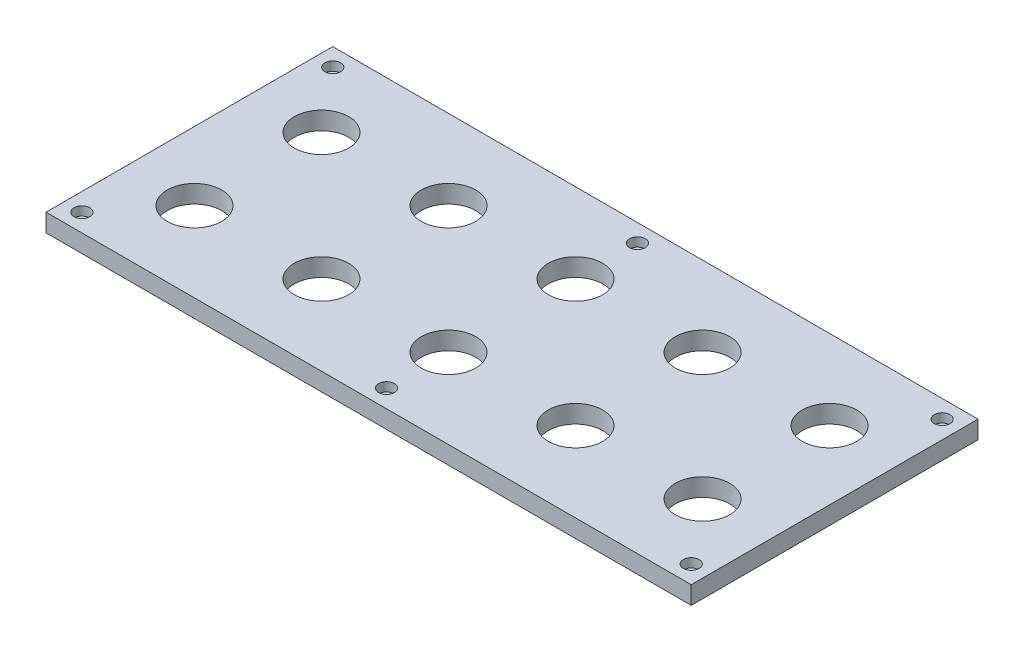
SolidWorks part; units mm, degrees
material "Ceramic Porcelain"
ref_plane "Front Plane" through (0, 0, 0) normal (0, 0, 1) x (1, 0, 0)
ref_plane "Top Plane" through (0, 0, 0) normal (0, 1, 0) x (1, 0, 0)
ref_plane "Right Plane" through (0, 0, 0) normal (1, 0, 0) x (0, 0, -1)
sketch "Sketch1" plane through (0, 0, 0) normal (0, 1, 0) x (1, 0, 0)
  line L1 (228.6, 101.6) -> (-228.6, 101.6)
  line L2 (228.6, 101.6) -> (228.6, -101.6)
  line L3 (228.6, -101.6) -> (-228.6, -101.6)
  line L4 (-228.6, 101.6) -> (-228.6, -101.6)
  line L5 (0, -101.6) -> (0, 101.6) construction
  line L6 (228.6, 0) -> (-228.6, 0) construction
  point P0 (0, 0)
  dimension "D1" = 457.2
  dimension "D2" = 203.2
extrude "Boss-Extrude1" add sketch "Sketch1" against normal blind 12.7
sketch "Sketch2" plane through (0, 0, 0) normal (0, 1, 0) x (1, 0, 0)
  circle A0 centre (-180, 45) radius 19.304 construction
  circle A1 centre (-90, 45) radius 19.304 construction
  circle A2 centre (0, 45) radius 19.304 construction
  circle A3 centre (-180, -45) radius 19.304 construction
  circle A4 centre (-90, -45) radius 19.304 construction
  circle A5 centre (0, -45) radius 19.304 construction
  circle A6 centre (90, -45) radius 19.304 construction
  circle A7 centre (90, 45) radius 19.304 construction
  circle A8 centre (180, 45) radius 19.304 construction
  circle A9 centre (180, -45) radius 19.304 construction
  circle A10 centre (-180, 45) radius 19.304
  circle A11 centre (-90, 45) radius 19.304
  circle A12 centre (0, 45) radius 19.304
  circle A13 centre (-180, -45) radius 19.304
  circle A14 centre (-90, -45) radius 19.304
  circle A15 centre (0, -45) radius 19.304
  circle A16 centre (90, -45) radius 19.304
  circle A17 centre (90, 45) radius 19.304
  circle A18 centre (180, 45) radius 19.304
  circle A19 centre (180, -45) radius 19.304
  point P0 (0, 88.9)
  point P2 (-215.9, 88.9)
  point P4 (215.9, 88.9)
  point P6 (215.9, -88.9)
  point P8 (0, -88.9)
  point P10 (-215.9, -88.9)
extrude "Cut-Extrude1" cut sketch "Sketch2" against normal up to next
hole_wizard "CBORE for 1/4 Socket Head Cap Screw1" positions "Sketch5" profile "Sketch6" counterbore size "1/4" standard "ANSI Inch" end condition up to next
sketch "Sketch5" plane through (0, 0, 0) normal (0, 1, 0) x (1, 0, 0)
  point P0 (-215.9, -88.9)
  point P3 (0, -88.9)
  point P6 (215.9, -88.9)
  point P9 (215.9, 88.9)
  point P12 (0, 88.9)
  point P15 (-215.9, 88.9)
sketch "Sketch6" plane through (-215.9, 0, 88.9) normal (1, 0, 0) x (0, 0, 1)
  line L0 (0, 0) -> (0, 12.7)
  line L1 (0, 12.7) -> (3.3782, 12.7)
  line L3 (3.3782, 12.7) -> (3.3782, 6.35)
  line L4 (3.3782, 6.35) -> (5.5562, 6.35)
  line L5 (5.5562, 6.35) -> (5.5562, 0)
  line L7 (5.5562, 0) -> (0, 0)
  line L11 (0, -6.35) -> (0, 107.95) construction
  dimension "Thru Hole Dia." = 6.7564
  dimension "Thru Hole Depth" = 12.7
  dimension "C'Bore Dia." = 11.1125
  dimension "C'Bore Depth" = 6.35
